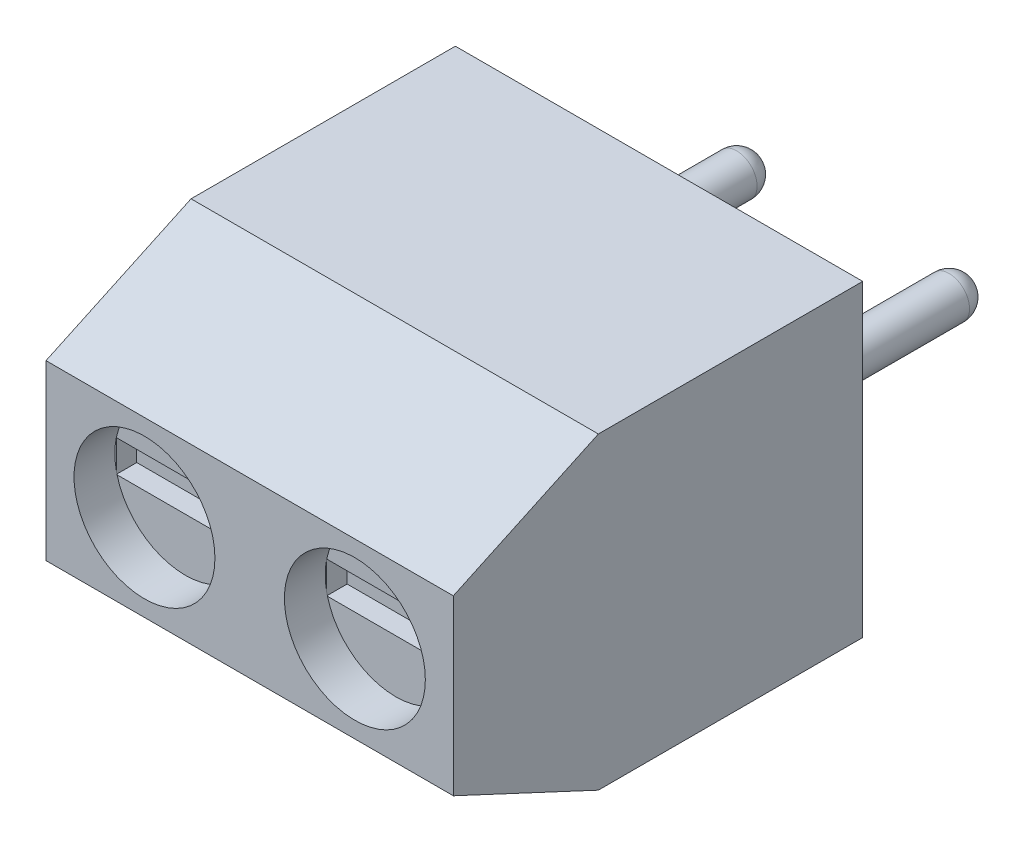
SolidWorks part; units mm, degrees
ref_plane "Face" through (0, 0, 0) normal (0, 0, 1) x (1, 0, 0)
ref_plane "Dessus" through (0, 0, 0) normal (0, 1, 0) x (1, 0, 0)
ref_plane "Droite" through (0, 0, 0) normal (1, 0, 0) x (0, 0, -1)
sketch "Esquisse1" plane through (0, 0, 0) normal (0, 0, 1) x (1, 0, 0)
  line L1 (0, 0) -> (9.97, 0)
  line L2 (0, 0) -> (0, 7.55)
  line L3 (0, 7.55) -> (9.97, 7.55)
  line L4 (9.97, 0) -> (9.97, 7.55)
  dimension "D1" = 9.97
  dimension "D2" = 7.55
extrude "Extrusion1" add sketch "Esquisse1" along normal blind 10.02
chamfer "Chanfrein1" distance 3.55 angle 25 2 edges at (4.985, 7.55, 10.02) (4.985, 0, 10.02)
sketch "Esquisse2" plane through (0, 0, 10.02) normal (0, 0, 1) x (1, 0, 0)
  line L0 (0, 3.775) -> (9.97, 3.775) construction
  line L1 (0, 5.8946) -> (0, 1.6554) construction
  line L2 (9.97, 1.6554) -> (9.97, 5.8946) construction
  line L3 (4.985, 5.8946) -> (4.985, 1.6554) construction
  line L4 (9.97, 5.8946) -> (0, 5.8946) construction
  line L5 (0, 1.6554) -> (9.97, 1.6554) construction
  circle A0 centre (2.4101, 3.775) radius 1.725
  circle A1 centre (7.5599, 3.775) radius 1.725
  dimension "D1" = 3.45
extrude "Enlèv. mat.-Extru.1" cut sketch "Esquisse2" against normal blind 1
sketch "Esquisse3" plane through (0, 0, 0) normal (0, -1, 0) x (1, 0, 0)
  line L0 (4.985, 6.47) -> (4.985, 0) construction
  line L1 (9.97, 6.47) -> (0, 6.47) construction
  line L2 (0, 0) -> (9.97, 0) construction
  line L4 (9.435, 5.8) -> (5.435, 5.8)
  line L5 (9.435, 5.8) -> (9.435, 0.8)
  line L6 (9.435, 0.8) -> (5.435, 0.8)
  line L7 (5.435, 5.8) -> (5.435, 0.8)
  line L8 (4.535, 5.8) -> (0.535, 5.8)
  line L9 (4.535, 5.8) -> (4.535, 0.8)
  line L10 (4.535, 0.8) -> (0.535, 0.8)
  line L11 (0.535, 5.8) -> (0.535, 0.8)
  dimension "D1" = 5
  dimension "D2" = 4
  dimension "D3" = 0.8
  dimension "D4" = 0.9
extrude "Enlèv. mat.-Extru.2" cut sketch "Esquisse3" against normal blind 1.6
sketch "Esquisse4" plane through (0, 1.6, 0) normal (0, -1, 0) x (1, 0, 0)
  line L0 (9.97, 3.235) -> (0, 3.235) construction
  line L1 (9.97, 6.47) -> (9.97, 0) construction
  line L2 (0, 6.47) -> (0, 0) construction
  line L3 (7.435, 5.8) -> (7.435, 0.8) construction
  line L4 (9.435, 5.8) -> (5.435, 5.8) construction
  line L5 (5.435, 0.8) -> (9.435, 0.8) construction
  line L6 (2.535, 5.8) -> (2.535, 0.8) construction
  line L7 (4.535, 5.8) -> (0.535, 5.8) construction
  line L8 (0.535, 0.8) -> (4.535, 0.8) construction
  circle A0 centre (7.435, 3.235) radius 1.675
  circle A1 centre (2.535, 3.235) radius 1.675
  dimension "D1" = 3.35
extrude "Enlèv. mat.-Extru.3" cut sketch "Esquisse4" against normal blind 1.6
sketch "Esquisse5" plane through (0, 0, 0) normal (0, 0, -1) x (-1, 0, 0)
  line L0 (-9.97, 3.775) -> (0, 3.775) construction
  line L1 (-9.97, 0) -> (-9.97, 7.55) construction
  line L2 (0, 7.55) -> (0, 0) construction
  line L3 (-4.985, 7.55) -> (-4.985, 0) construction
  line L4 (-9.97, 7.55) -> (0, 7.55) construction
  line L5 (0, 0) -> (-9.97, 0) construction
  circle A0 centre (-7.585, 3.775) radius 0.5
  circle A1 centre (-2.385, 3.775) radius 0.5
  dimension "D1" = 1
  dimension "D2" = 5.2
extrude "Extrusion2" add sketch "Esquisse5" along normal blind 5
fillet "Congé1" radius 0.5 2 edges at (1.885, 3.775, -5) (7.085, 3.775, -5)
sketch "Esquisse7" plane through (0, 0, 9.02) normal (0, 0, 1) x (1, 0, 0)
  line L1 (0.721, 4.1248) -> (4.0806, 4.1248)
  line L2 (0.721, 4.1248) -> (0.721, 3.3447)
  line L3 (0.721, 3.3447) -> (4.0806, 3.3447)
  line L4 (4.0806, 4.1248) -> (4.0806, 3.3447)
  line L5 (5.8707, 4.1248) -> (9.2304, 4.1248)
  line L6 (5.8707, 4.1248) -> (5.8707, 3.3447)
  line L7 (5.8707, 3.3447) -> (9.2304, 3.3447)
  line L8 (9.2304, 4.1248) -> (9.2304, 3.3447)
  circle A0 centre (2.4101, 3.775) radius 1.725 construction
  circle A1 centre (7.5599, 3.775) radius 1.725 construction
extrude "Enlèv. mat.-Extru.4" cut sketch "Esquisse7" against normal blind 0.5
sketch "Esquisse8" plane through (0, 3.2, 0) normal (0, -1, 0) x (1, 0, 0)
  line L1 (0.9436, 3.7576) -> (4.1396, 3.7576)
  line L2 (0.9436, 3.7576) -> (0.9436, 2.7545)
  line L3 (0.9436, 2.7545) -> (4.1396, 2.7545)
  line L4 (4.1396, 3.7576) -> (4.1396, 2.7545)
  line L5 (5.8436, 3.7576) -> (9.0396, 3.7576)
  line L6 (5.8436, 3.7576) -> (5.8436, 2.7545)
  line L7 (5.8436, 2.7545) -> (9.0396, 2.7545)
  line L8 (9.0396, 3.7576) -> (9.0396, 2.7545)
  circle A0 centre (2.535, 3.235) radius 1.675 construction
  circle A1 centre (7.435, 3.235) radius 1.675 construction
extrude "Enlèv. mat.-Extru.5" cut sketch "Esquisse8" against normal blind 0.5
